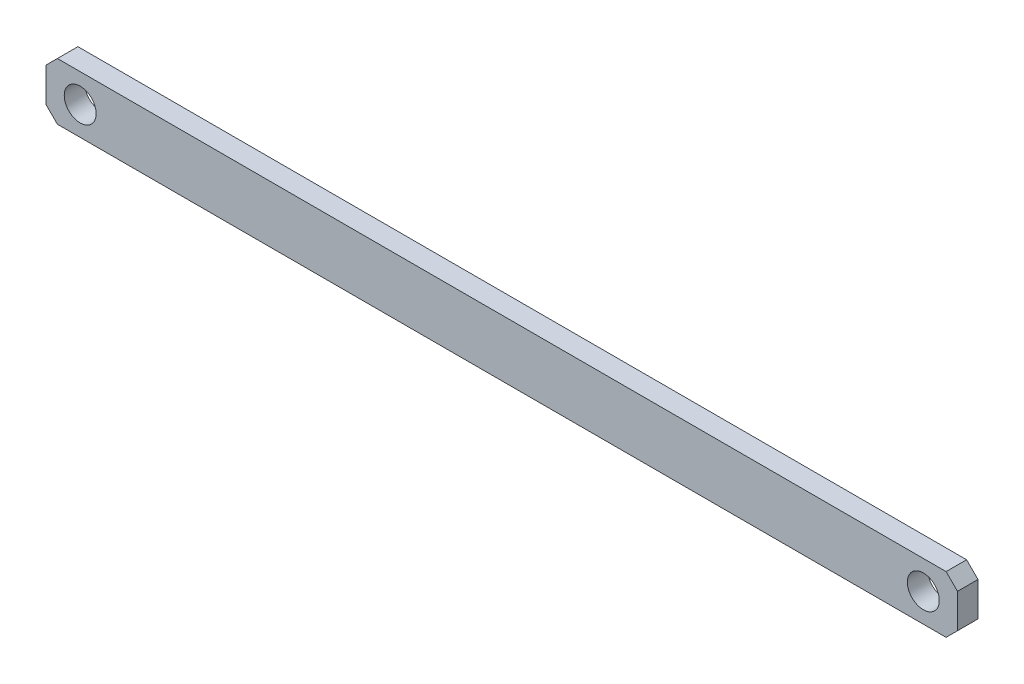
SolidWorks part; units mm, degrees
ref_plane "前基準面" through (0, 0, 0) normal (0, 0, 1) x (1, 0, 0)
ref_plane "上基準面" through (0, 0, 0) normal (0, 1, 0) x (1, 0, 0)
ref_plane "右基準面" through (0, 0, 0) normal (1, 0, 0) x (0, 0, -1)
sketch "草圖1" plane through (0, 0, 0) normal (0, 0, 1) x (1, 0, 0)
  line L0 (195, 12.5) -> (200, 7.5)
  line L5 (-195, -12.5) -> (195, -12.5)
  line L6 (-200, -7.5) -> (-200, 7.5)
  line L7 (-195, 12.5) -> (195, 12.5)
  line L8 (200, -7.5) -> (200, 7.5)
  line L9 (-200, -12.5) -> (200, 12.5) construction
  line L10 (-200, 12.5) -> (200, -12.5) construction
  line L11 (195, -12.5) -> (200, -7.5)
  line L12 (-195, -12.5) -> (-200, -7.5)
  line L13 (-200, 7.5) -> (-195, 12.5)
  line L14 (0, -34.0481) -> (0, 33.684) construction
  circle A0 centre (185, 0) radius 7
  circle A1 centre (-185, 0) radius 7
  point P0 (0, 0)
  dimension "D3" = 14
  dimension "D1" = 25
  dimension "D2" = 400
  dimension "15" = 15
extrude "填料-伸長1" add sketch "草圖1" along normal mid plane 9
